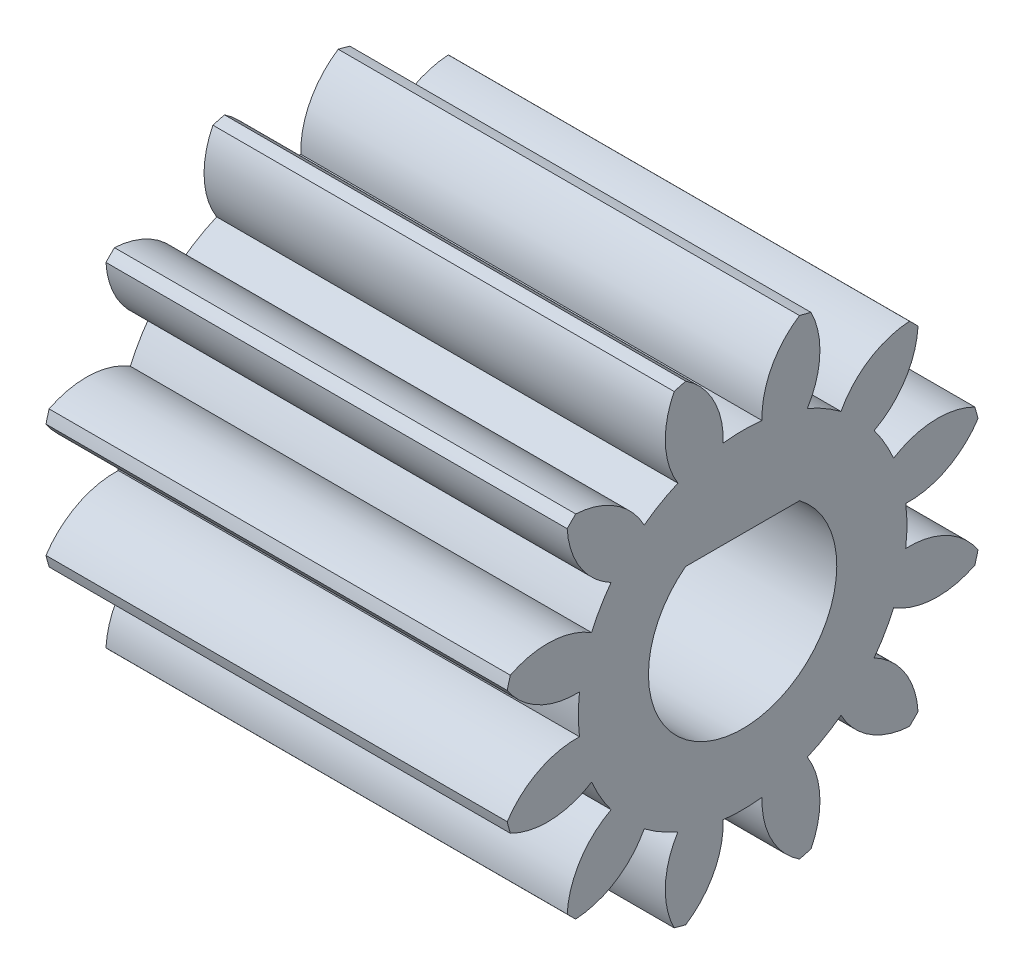
SolidWorks part; units mm, degrees
ref_plane "Plane1" through (0, 0, 0) normal (0, 0, 1) x (1, 0, 0)
ref_plane "Plane2" through (0, 0, 0) normal (0, 1, 0) x (1, 0, 0)
ref_plane "Plane3" through (0, 0, 0) normal (1, 0, 0) x (0, 0, -1)
other "Configuration Table"
sketch "HoldingSke" plane through (0, 0, 0) normal (0, 1, 0) x (1, 0, 0)
  line L0 (0, 0) -> (1.0868, -0.231)
  line L1 (-15, 0) -> (100, 0) construction
  line L2 (0, 0) -> (-2.1039, 2.3779)
  line L3 (0, 0) -> (-11.863, 4.5341)
  line L4 (0, 0) -> (8.4473, 1.7955)
  line L5 (0, 0) -> (-46.8476, -17.4728)
  line L6 (0, 0) -> (-9.9476, -6.7116)
  line L7 (-2.1039, 2.3779) -> (8.6586, 51.2059)
  line L8 (-76.2, 54.61) -> (-75.3, 54.61)
  line L9 (-71.009, 38.7566) -> (-53.1078, 45.2721)
  line L10 (-76.2, 71.12) -> (104.1128, 71.12)
  line L11 (0, 0) -> (-12, 0)
  line L12 (-76.2, 101.6) -> (-76.166, 101.6)
  line L13 (24.9733, 27.94) -> (52.9518, 28.4284)
  line L14 (24.9733, 27.94) -> (24.9743, 27.94)
  line L15 (24.9733, 27.94) -> (100.4006, 29.5858)
  line L16 (-63.627, -0.9) -> (-12.827, -0.9)
  circle A0 centre (0, 0) radius 2.5
  circle A1 centre (0, 0) radius 4.274
  circle A2 centre (0, 0) radius 37.5
  circle A3 centre (0, 0) radius 2.5
  dimension "MHD" = 8.548
  dimension "Hub_dia" = 75
  dimension "Bore" = 5
  dimension "MBD" = 5
  dimension "Num_teeth" = 12
  dimension "Pitch" = 1.1111
  dimension "Overall_len" = 50
  dimension "Show_teeth" = 12
  dimension "Thickness" = 12
  dimension "OAL" = 50.0001
  dimension "T_dim" = 0.9
  dimension "Ap" = 20
  dimension "H" = 19.05
  dimension "Pitch_radius" = 180.3128
  dimension "Width" = 12
  dimension "Backlash" = 0.034
  dimension "Addendum_fac" = 1
  dimension "Dedendum_fac" = 1.25
  dimension "Clearance_fac" = 0.25
  dimension "Dedendum_add" = 0.001
  dimension "Module" = 0.9
sketch "BasProSke" plane through (0, 0, 0) normal (0, 1, 0) x (1, 0, 0)
  line L0 (-10, 0) -> (60, 0) construction
  line L1 (0, 0) -> (0, 6.3)
  line L2 (0, 0) -> (12, 0)
  line L3 (12, 0) -> (12, 6.3)
  line L4 (12, 6.3) -> (0, 6.3)
  dimension "Thickness" = 12
  dimension "Diameter" = 12.6
revolve "Base-Revolve" add sketch "BasProSke" angle 360 about L0
sketch "TooCutSke" plane through (0, 0, 0) normal (1, 0, 0) x (0, 0, -1)
  line L1 (0, 0) -> (0, 107) construction
  line L2 (0, 0) -> (-0.7643, 5.3456) construction
  line L3 (0, 0) -> (-2.7752, 10.3572) construction
  line L4 (-0.7643, 5.3456) -> (-1.3876, 5.1786) construction
  arc A0 (0.5057, 4.244) -> (-0.5057, 4.244) centre (0, 0) ccw
  arc A1 (1.5081, 6.143) -> (-1.5081, 6.143) centre (0, 0) ccw
  circle A2 centre (0, 0) radius 5.4 construction
  circle A3 centre (0, 0) radius 5.0743 construction
  arc A4 (-0.5057, 4.244) -> (-1.5081, 6.143) centre (-2.6644, 4.3185) ccw
  arc A5 (1.5081, 6.143) -> (0.5057, 4.244) centre (2.6644, 4.3185) ccw
  dimension "Root_dia" = 8.548
  dimension "Overcut_dia" = 12.6508
  dimension "Pitch_dia" = 10.8
  dimension "Base_dia" = 10.1487
  dimension "Flank_rad" = 2.16
  dimension "Half_ang" = 15
  dimension "Half_CT" = 0.6453
extrude "ToothCut" cut sketch "TooCutSke" along normal through all
fillet "Breaks" [suppressed] radius 0.018
fillet "RootFillets" [suppressed] radius 0.226
pattern_circular "TeethCuts" count 12 every 30 about axis through (-10, 0, 0) along (1, 0, 0) of "ToothCut", "RootFillets", "Breaks"
sketch "HubNeaOneSke" plane through (0, 0, 0) normal (-1, 0, 0) x (0, 0, 1)
  circle A0 centre (0, 0) radius 4.274
  dimension "Diameter" = 8.548
extrude "HubNearOne" [suppressed] add sketch "HubNeaOneSke" along normal blind 38.0001
sketch "HubNeaBotSke" plane through (0, 0, 0) normal (-1, 0, 0) x (0, 0, 1)
  circle A0 centre (0, 0) radius 4.274
  dimension "Diameter" = 8.548
extrude "HubNearBoth" [suppressed] add sketch "HubNeaBotSke" along normal blind 19
ref_plane "FarPln" through (12, 0, 0) normal (1, 0, 0) x (0, 0, -1)
sketch "HubFarSke" plane through (12, 0, 0) normal (1, 0, 0) x (0, 0, -1)
  circle A0 centre (0, 0) radius 4.274
  dimension "Diameter" = 8.548
extrude "HubFar" [suppressed] add sketch "HubFarSke" along normal blind 19
sketch "BorSke" plane through (0, 0, 0) normal (1, 0, 0) x (0, 0, -1)
  line L0 (-1.5, 2) -> (1.5, 2) construction
  line L1 (0, 2) -> (0, -2.5) construction
  line L2 (-1.4832, 1.95) -> (1.4832, 1.95)
  arc A0 (-1.5, 2) -> (1.5, 2) centre (0, 0) ccw construction
  arc A1 (-1.4832, 1.95) -> (1.4832, 1.95) centre (0, 0) ccw
  dimension "Diameter" = 5
  dimension "D1" = 4.5
  dimension "D2" = 0.05
extrude "Bore" cut sketch "BorSke" along normal mid plane 100.0001
sketch "KeySke" plane through (0, 0, 0) normal (1, 0, 0) x (0, 0, -1)
  line L0 (-1, 0) -> (-1, 3.4)
  line L1 (-1, 3.4) -> (1, 3.4)
  line L2 (1, 3.4) -> (1, 0)
  line L3 (0, 0) -> (0, 34) construction
  line L4 (-1, 0) -> (1, 0)
  dimension "Offset" = 3.4
  dimension "Width" = 2
extrude "Keyway" [suppressed] cut sketch "KeySke" along normal mid plane 100.0001
pattern_circular "Keyway2" [suppressed] count 2 every 90 about axis through (-10, 0, 0) along (1, 0, 0)
equation "' \"Module@HoldingSke\" = 6.35"
equation "' \"Num_teeth@HoldingSke\" = 12"
equation "' \"Ap@HoldingSke\" =  20"
equation "' \"Ap@HoldingSke\" = 20"
equation "' \"Width@HoldingSke\" = 0.5 * 25.4"
equation "' \"Hub_dia@HoldingSke\"= 1 * 25.4"
equation "' \"Hub_dia@HoldingSke\" = 1 * 25.4"
equation "' \"Overall_len@HoldingSke\" = 1.0 * 25.4"
equation "' \"Bore@HoldingSke\" = 0.75 * 25.4"
equation "' \"T_dim@HoldingSke\" = 0.1 * 25.4"
equation "' \"Width@KeySke\" = 0.25 * 25.4"
equation "' \"Show_teeth@HoldingSke\" = 13"
equation "' \"Backlash@HoldingSke\" = 0.009 * 25.4"
equation "' \"Addendum_fac@HoldingSke\" = 1.0"
equation "' \"Dedendum_fac@HoldingSke\" = 1.25"
equation "' \"Dedendum_add@HoldingSke\" = 0.00005 * 25.4"
equation "' \"Clearance_fac@HoldingSke\" = 0.25"
equation "\"Pitch@HoldingSke\" = 1 / \"Module@HoldingSke\""
equation "\"Overcut_dia@TooCutSke\" = (\"Num_teeth@HoldingSke\" + 2 * \"Addendum_fac@HoldingSke\") / \"Pitch@HoldingSke\" + 0.002 * 25.4"
equation "\"Pitch_dia@TooCutSke\" = \"Num_teeth@HoldingSke\" / \"Pitch@HoldingSke\""
equation "\"Base_dia@TooCutSke\" = \"Num_teeth@HoldingSke\" / \"Pitch@HoldingSke\" * cos((\"Ap@HoldingSke\"  * 3.14159265 / 180))"
equation "\"Root_dia@TooCutSke\" = (\"Num_teeth@HoldingSke\" + 2) / \"Pitch@HoldingSke\" - 2 * (\"Addendum_fac@HoldingSke\" + \"Dedendum_fac@HoldingSke\") / \"Pitch@HoldingSke\" - \"Dedendum_add@HoldingSke\" * 2"
equation "\"Half_ang@TooCutSke\" = 180 / \"Num_teeth@HoldingSke\""
equation "\"Half_CT@TooCutSke\" = \"Num_teeth@HoldingSke\" / \"Pitch@HoldingSke\" * sin((3.14159265 / 2 / \"Num_teeth@HoldingSke\")) / 2 - 7 * \"Backlash@HoldingSke\" / 4"
equation "\"Flank_rad@TooCutSke\" = \"Num_teeth@HoldingSke\" / \"Pitch@HoldingSke\" / 5"
equation "\"Radius@RootFillets\" = \"Clearance_fac@HoldingSke\" / \"Pitch@HoldingSke\" + \"Dedendum_add@HoldingSke\""
equation "\"Break_rad@Breaks\" = 0.02 / \"Pitch@HoldingSke\""
equation "\"Thickness@HoldingSke\" = \"Width@HoldingSke\""
equation "\"OAL@HoldingSke\" = \"Thickness@HoldingSke\""
equation "\"MHD@HoldingSke\" = (\"Num_teeth@HoldingSke\" + 2) / \"Pitch@HoldingSke\" - 2 * (\"Addendum_fac@HoldingSke\" + \"Dedendum_fac@HoldingSke\")  / \"Pitch@HoldingSke\" - \"Dedendum_add@HoldingSke\" * 2"
equation "\"MBD@HoldingSke\" = (\"Num_teeth@HoldingSke\" + 2) / \"Pitch@HoldingSke\" - 2 * (\"Addendum_fac@HoldingSke\" + \"Dedendum_fac@HoldingSke\")  / \"Pitch@HoldingSke\" - \"Dedendum_add@HoldingSke\" * 2 - 0.002 * 25.4"
equation "\"MHD@HoldingSke\" = ((sgn( \"MHD@HoldingSke\" - \"Hub_dia@HoldingSke\" )-1)*( \"MHD@HoldingSke\" - \"Hub_dia@HoldingSke\" ))/-2+ \"Hub_dia@HoldingSke\""
equation "\"MBD@HoldingSke\" = ((sgn( \"MBD@HoldingSke\" - \"Bore@HoldingSke\" )-1)*( \"MBD@HoldingSke\" - \"Bore@HoldingSke\" ))/-2+ \"Bore@HoldingSke\""
equation "\"OAL@HoldingSke\" = ((sgn( \"OAL@HoldingSke\" - \"Overall_len@HoldingSke\" )+1)*( \"OAL@HoldingSke\" - \"Overall_len@HoldingSke\" ))/2 + \"Overall_len@HoldingSke\" + 0.000002 * 25.4"
equation "\"Num_teeth@TeethCuts\" = int( \"Show_teeth@HoldingSke\" ) + 1"
equation "\"Num_teeth@TeethCuts\" = ((sgn( \"Num_teeth@TeethCuts\" - \"Num_teeth@HoldingSke\" )-1)*( \"Num_teeth@TeethCuts\" - \"Num_teeth@HoldingSke\" ))/-2+ \"Num_teeth@HoldingSke\""
equation "\"Num_teeth@TeethCuts\" = ((sgn( \"Num_teeth@TeethCuts\" - 2.0)+1)*( \"Num_teeth@TeethCuts\" - 2.0))/2 +2.0"
equation "\"Angle@TeethCuts\" = 360.0 / \"Num_teeth@HoldingSke\""
equation "\"Diameter@BasProSke\" = (\"Num_teeth@HoldingSke\" + 2 * \"Addendum_fac@HoldingSke\") / \"Pitch@HoldingSke\""
equation "\"Thickness@BasProSke\"  = \"Thickness@HoldingSke\""
equation "' \"Fillet_rad@BasProSke\" =  \"Thickness@HoldingSke\" * 0.05"
equation "' \"Fillet_rad@BasProSke\" = \"Thickness@HoldingSke\" * 0.05"
equation "\"MHD@HoldingSke\" = ((sgn( \"MHD@HoldingSke\" - \"Root_dia@TooCutSke\" )-1)*( \"MHD@HoldingSke\" - \"Root_dia@TooCutSke\" ))/-2+ \"Root_dia@TooCutSke\""
equation "\"Diameter@HubNeaOneSke\" = \"MHD@HoldingSke\""
equation "\"Length@HubNearOne\" = \"OAL@HoldingSke\" - \"Thickness@BasProSke\""
equation "\"Diameter@HubNeaBotSke\" = \"MHD@HoldingSke\""
equation "\"Length@HubNearBoth\" = ( \"OAL@HoldingSke\" - \"Thickness@BasProSke\" ) / 2.0"
equation "\"Thickness@FarPln\" = \"Thickness@BasProSke\""
equation "\"Diameter@HubFarSke\" = \"MHD@HoldingSke\""
equation "\"Length@HubFar\" = ( \"OAL@HoldingSke\" - \"Thickness@BasProSke\" ) / 2.0"
equation "\"Diameter@BorSke\" = \"MBD@HoldingSke\""
equation "\"D1@Bore\" = \"OAL@HoldingSke\" * 2.0"
equation "\"D1@Keyway\" = \"OAL@HoldingSke\" * 2.0"
equation "\"Offset@KeySke\" = \"T_dim@HoldingSke\" + \"MBD@HoldingSke\" / 2.0"
